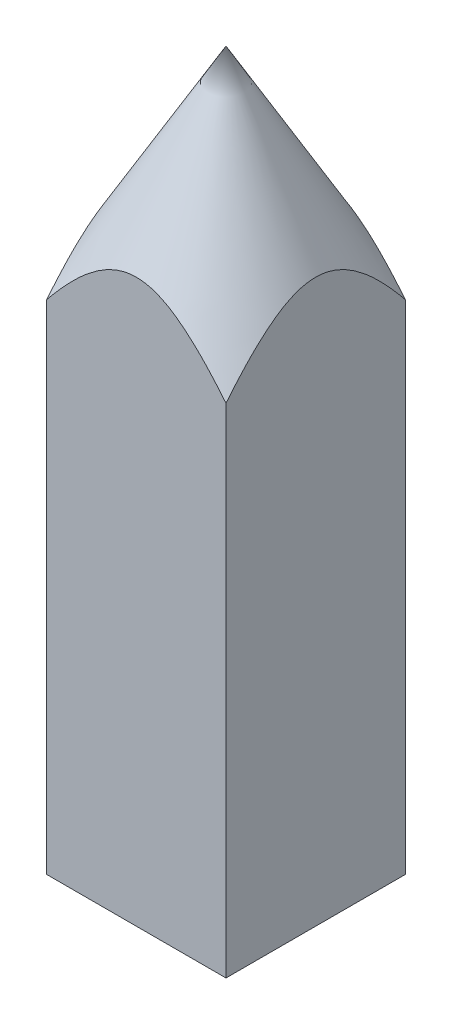
SolidWorks part; units mm, degrees
ref_plane "Front" through (0, 0, 0) normal (0, 0, 1) x (1, 0, 0)
ref_plane "Top" through (0, 0, 0) normal (0, 1, 0) x (1, 0, 0)
ref_plane "Right" through (0, 0, 0) normal (1, 0, 0) x (0, 0, -1)
sketch "Sketch4" plane through (0, 0, 0) normal (0, 0, 1) x (1, 0, 0)
  line L0 (0, 0) -> (0, 40)
  line L1 (0, 40) -> (7.0711, 27.7526)
  line L2 (7.0711, 27.7526) -> (7.0711, 0)
  line L4 (7.0711, 0) -> (0, 0)
  dimension "D1" = 40
  dimension "D2" = 7.0711
  dimension "D3" = 30
revolve "Revolve1" add sketch "Sketch4" angle 360 about L0
sketch "Sketch5" plane through (0, 0, 0) normal (0, 1, 0) x (1, 0, 0)
  line L1 (-5, 5) -> (5, 5)
  line L2 (-5, 5) -> (-5, -5)
  line L3 (-5, -5) -> (5, -5)
  line L4 (5, 5) -> (5, -5)
  circle A4 centre (0, 0) radius 7.0711 construction
extrude "Extrude2" cut sketch "Sketch5" along normal through all flip side to cut
